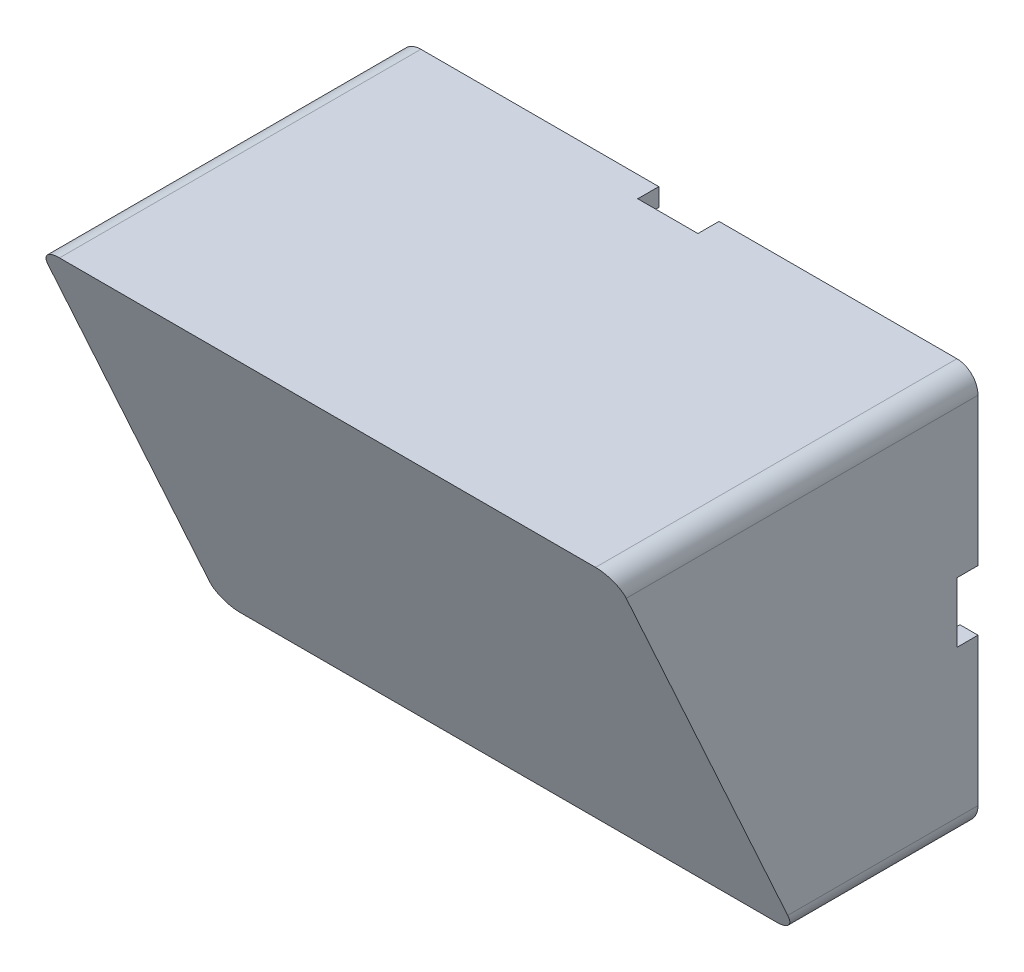
SolidWorks part; units mm, degrees
ref_plane "Alzado" through (0, 0, 0) normal (0, 0, 1) x (1, 0, 0)
ref_plane "Planta" through (0, 0, 0) normal (0, 1, 0) x (1, 0, 0)
ref_plane "Vista lateral" through (0, 0, 0) normal (1, 0, 0) x (0, 0, -1)
sketch "Croquis1" plane through (0, 0, 0) normal (0, 0, 1) x (1, 0, 0)
  line L1 (0, 0) -> (96, 0)
  line L2 (0, 0) -> (0, 66)
  line L3 (0, 66) -> (96, 66)
  line L4 (96, 0) -> (96, 66)
extrude "Saliente-Extruir1" add sketch "Croquis1" along normal blind 60
sketch "Croquis2" plane through (96, 0, 0) normal (1, 0, 0) x (0, 0, -1)
  line L0 (-60, 66) -> (-30, 0)
  line L3 (-60, 0) -> (-60, 66) construction
  line L4 (-60, 0) -> (0, 0) construction
  line L5 (-30, 0) -> (-60, 0)
  line L6 (-60, 0) -> (-60, 66)
extrude "Cortar-Extruir1" cut sketch "Croquis2" against normal blind 100
shell "Vaciado1" thickness 3
sketch "Croquis3" plane through (0, 0, 0) normal (0, 0, -1) x (-1, 0, 0)
  line L0 (-48, 63) -> (-48, 66) construction
  line L1 (-93, 63) -> (-3, 63) construction
  line L2 (-96, 66) -> (0, 66) construction
  line L3 (-3, 3) -> (-93, 3) construction
  line L4 (-48, 66) -> (-43, 66)
  line L5 (-48, 66) -> (-48, 63)
  line L6 (-48, 63) -> (-43, 63)
  line L7 (-43, 66) -> (-43, 63)
  line L8 (-48, 66) -> (-53, 66)
  line L10 (-48, 63) -> (-53, 63)
  line L11 (-53, 66) -> (-53, 63)
  line L12 (-43, 3) -> (-53, 3)
  line L13 (-43, 3) -> (-43, 0)
  line L14 (-43, 0) -> (-53, 0)
  line L15 (-53, 3) -> (-53, 0)
  line L16 (0, 0) -> (-96, 0) construction
  line L17 (0, 33) -> (-3, 33) construction
  line L18 (0, 66) -> (0, 0) construction
  line L19 (-3, 3) -> (-3, 63) construction
  line L20 (-3, 63) -> (-3, 3) construction
  line L21 (0, 33) -> (-3, 33)
  line L22 (0, 33) -> (0, 28)
  line L23 (0, 28) -> (-3, 28)
  line L24 (-3, 33) -> (-3, 28)
  line L25 (-93, 3) -> (-93, 63) construction
  line L27 (0, 33) -> (0, 38)
  line L28 (0, 38) -> (-3, 38)
  line L29 (-3, 33) -> (-3, 38)
  line L30 (-93, 38) -> (-96, 38)
  line L31 (-93, 38) -> (-93, 28)
  line L32 (-93, 28) -> (-96, 28)
  line L33 (-96, 38) -> (-96, 28)
  line L34 (-96, 0) -> (-96, 66) construction
  line M11 (0, 0) -> (0, 66)
  line M12 (0, 66) -> (-96, 66)
  line M13 (-96, 66) -> (-96, 0)
  line M14 (-96, 0) -> (0, 0)
  line M15 (-93, 63) -> (-3, 63)
  line M16 (-3, 63) -> (-3, 3)
  line M17 (-3, 3) -> (-93, 3)
  line M18 (-93, 3) -> (-93, 63)
extrude "Cortar-Extruir2" cut sketch "Croquis3" against normal blind 3.5 contours L28 L21 M11 M16 | L23 L21 M11 M16 | L7 L5 M12 M15 | L11 L5 M12 M15 | L15 L13 M17 M14 | L32 L30 M18 M13
fillet "Redondeo1" radius 3.5 4 edges at (0, 66, 30) (0, 0, 15) (96, 0, 15) (96, 66, 30)
